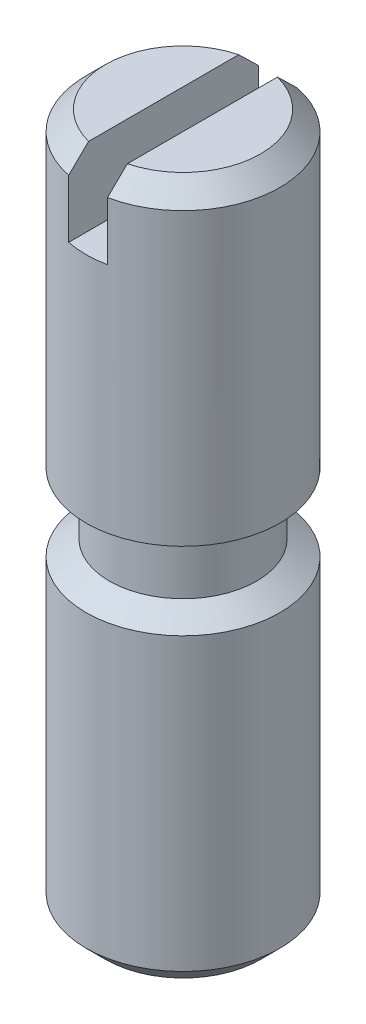
SolidWorks part; units mm, degrees
ref_plane "Vorne" through (0, 0, 0) normal (0, 0, 1) x (1, 0, 0)
ref_plane "Oben" through (0, 0, 0) normal (0, 1, 0) x (1, 0, 0)
ref_plane "Rechts" through (0, 0, 0) normal (1, 0, 0) x (0, 0, -1)
sketch "Skizze1" plane through (0, 0, 0) normal (0, 1, 0) x (1, 0, 0)
  circle A0 centre (0, 0) radius 2.5
  dimension "D1" = 5
extrude "Aufsatz-Linear austragen1" add sketch "Skizze1" along normal blind 18
cosmetic thread "Gewindedarstellung1" parameters "D2"=4
sketch "Skizze2" plane through (0, 18, 0) normal (0, 1, 0) x (1, 0, 0)
  line L0 (0, -55) -> (0, 55) construction
  line L1 (-0.5, 3.8045) -> (0.5, 3.8045)
  line L2 (-0.5, 3.8045) -> (-0.5, -4.947)
  line L3 (-0.5, -4.947) -> (0.5, -4.947)
  line L4 (0.5, 3.8045) -> (0.5, -4.947)
  dimension "D1" = 1
  dimension "D2" = 0.5
extrude "Schnitt-Linear austragen1" cut sketch "Skizze2" against normal blind 2
chamfer "Fase1" distance 0.5 angle 45 3 edges at (-2.5, 18, 0) (0, 0, 2.5) (2.5, 18, 0)
sketch "Skizze3" plane through (0, 0, 0) normal (0, 0, 1) x (1, 0, 0)
  line L0 (2.5, 10) -> (1.9, 10)
  line L1 (2.5, 0.5) -> (2.5, 17.5) construction
  line L2 (1.9, 10) -> (1.9, 8.4044)
  line L3 (1.9, 8.4044) -> (2.5, 8)
  line L4 (2.5, 8) -> (2.5, 10)
  line L5 (2, 18) -> (0.5, 18) construction
  line L6 (0, 12.2325) -> (0, 3.838) construction
  line L7 (0, -2.75) -> (0, 2.75) construction
  dimension "D1" = 2
  dimension "D2" = 8
  dimension "D3" = 0.6
revolve "Schnitt-Rotation1" cut sketch "Skizze3" angle 360 about L6
